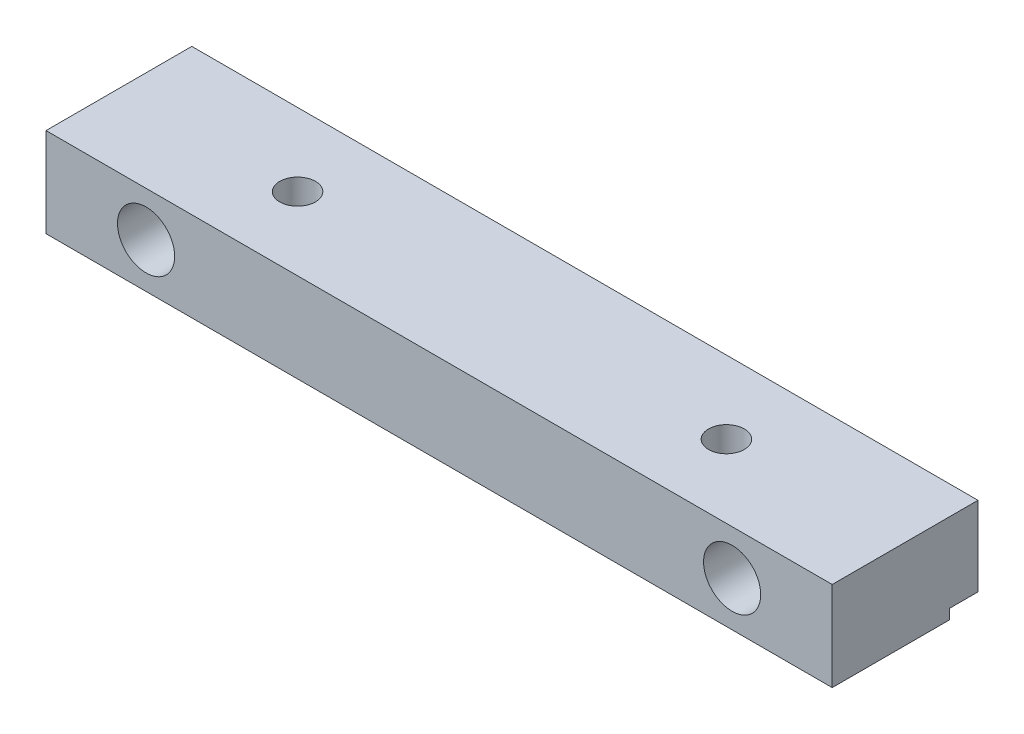
SolidWorks part; units mm, degrees
ref_plane "Front Plane" through (0, 0, 0) normal (0, 0, 1) x (1, 0, 0)
ref_plane "Top Plane" through (0, 0, 0) normal (0, 1, 0) x (1, 0, 0)
ref_plane "Right Plane" through (0, 0, 0) normal (1, 0, 0) x (0, 0, -1)
sketch "Sketch1" plane through (0, 0, 0) normal (0, 1, 0) x (1, 0, 0)
  line L1 (0, 0) -> (55, 0)
  line L2 (0, 0) -> (0, 10.2)
  line L3 (0, 10.2) -> (55, 10.2)
  line L4 (55, 0) -> (55, 10.2)
  dimension "D1" = 55
  dimension "D2" = 10.2
extrude "Boss-Extrude1" add sketch "Sketch1" along normal blind 6.25
hole_wizard "Ø4.0 (4) Diameter Hole1" positions "Sketch3" profile "Sketch2" hole size "Ø4.0" standard "Ansi Metric" end condition through all
sketch "Sketch3" plane through (0, 0, 0) normal (0, 0, 1) x (1, 0, 0)
  line L0 (0, 3.125) -> (7, 3.125) construction
  line L2 (7, 3.125) -> (48, 3.125) construction
  line L3 (48, 3.125) -> (55, 3.125) construction
  line L6 (55, 6.25) -> (55, 0) construction
  line L7 (0, 6.25) -> (0, 0) construction
  line L8 (0, 0) -> (55, 0) construction
  point P0 (7, 3.125)
  point P1 (48, 3.125)
  dimension "D1" = 3.125
  dimension "D2" = 41
sketch "Sketch2" plane through (7, 3.125, 0) normal (1, 0, 0) x (0, -1, 0)
  line L0 (0, 0) -> (0, 10.2)
  line L1 (0, 10.2) -> (2, 10.2)
  line L2 (2, 10.2) -> (2, 0)
  line L5 (2, 0) -> (0, 0)
  line L11 (0, -6.35) -> (0, 107.95) construction
  dimension "Thru Hole Dia." = 4
  dimension "Thru Hole Depth" = 10.2
ref_point "Point1"
ref_point "Point2"
hole_wizard "Ø2.5 (2.5) Diameter Hole1" positions "Sketch5" profile "Sketch4" hole size "Ø2.5" standard "Ansi Metric" end condition through all
sketch "Sketch5" plane through (0, 6.25, 0) normal (0, 1, 0) x (-1, 0, 0)
  line L0 (-7, -5.1) -> (-12.5, -5.1) construction
  line L2 (-12.5, -5.1) -> (-42.5, -5.1) construction
  line L3 (-42.5, -5.1) -> (-48, -5.1) construction
  point P0 (-12.5, -5.1)
  point P1 (-42.5, -5.1)
  dimension "D1" = 30
sketch "Sketch4" plane through (12.5, 6.25, -5.1) normal (1, 0, 0) x (0, 0, 1)
  line L0 (0, 0) -> (0, 6.25)
  line L1 (0, 6.25) -> (1.25, 6.25)
  line L2 (1.25, 6.25) -> (1.25, 0)
  line L5 (1.25, 0) -> (0, 0)
  line L11 (0, -6.35) -> (0, 107.95) construction
  dimension "Thru Hole Dia." = 2.5
  dimension "Thru Hole Depth" = 6.25
sketch "Sketch6" plane through (55, 0, 0) normal (1, 0, 0) x (0, 0, -1)
  line L1 (10.2, 0) -> (8.2, 0)
  line L2 (10.2, 0) -> (10.2, 0.7)
  line L3 (10.2, 0.7) -> (8.2, 0.7)
  line L4 (8.2, 0) -> (8.2, 0.7)
  dimension "D1" = 0.7
  dimension "D2" = 2
extrude "Cut-Extrude1" cut sketch "Sketch6" against normal through all
